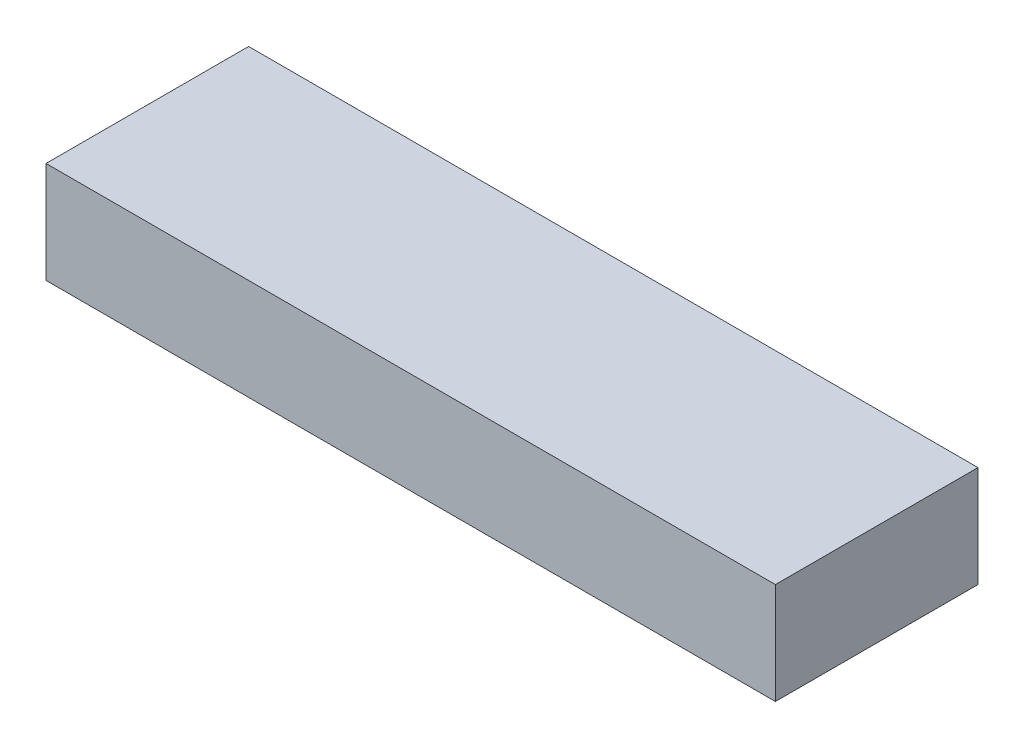
SolidWorks part; units mm, degrees
material "Liga 1060"
ref_plane "Plano frontal" through (0, 0, 0) normal (0, 0, 1) x (1, 0, 0)
ref_plane "Plano superior" through (0, 0, 0) normal (0, 1, 0) x (1, 0, 0)
ref_plane "Plano direito" through (0, 0, 0) normal (1, 0, 0) x (0, 0, -1)
sketch "Esboço1" plane through (0, 0, 0) normal (0, 1, 0) x (1, 0, 0)
  line L1 (-90, 25) -> (90, 25)
  line L2 (-90, 25) -> (-90, -25)
  line L3 (-90, -25) -> (90, -25)
  line L4 (90, 25) -> (90, -25)
  line L5 (-90, 25) -> (90, -25) construction
  line L6 (-90, -25) -> (90, 25) construction
  point P0 (0, 0)
  dimension "D1" = 180
  dimension "D2" = 50
extrude "Ressalto-extrusão1" add sketch "Esboço1" along normal blind 25
